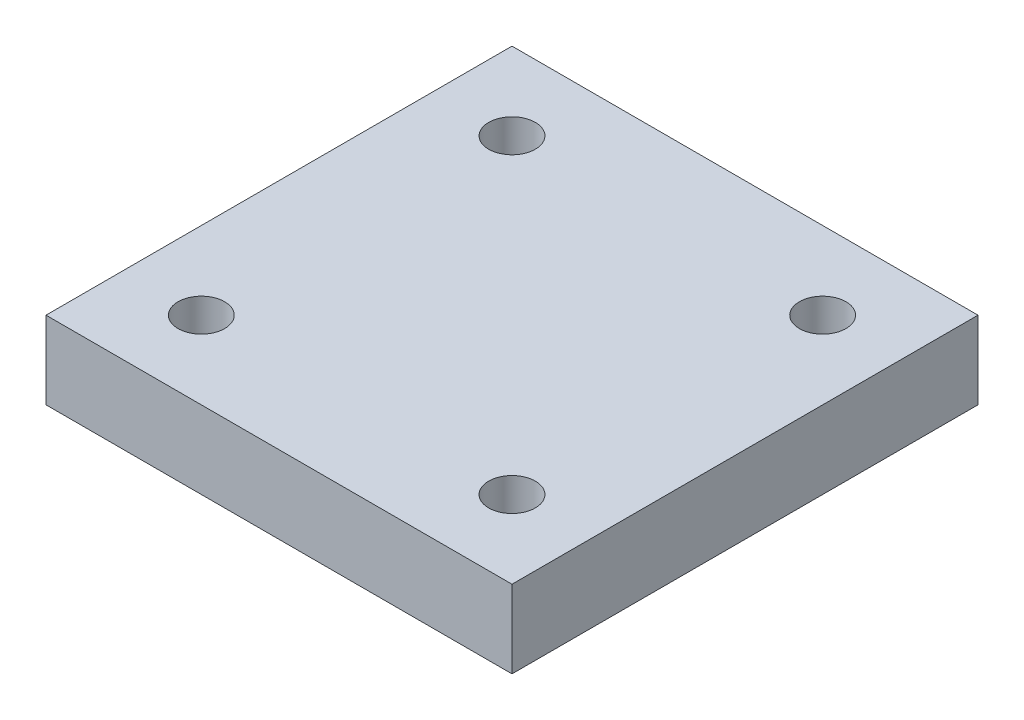
SolidWorks part; units mm, degrees
ref_plane "前视基准面" through (0, 0, 0) normal (0, 0, 1) x (1, 0, 0)
ref_plane "上视基准面" through (0, 0, 0) normal (0, 1, 0) x (1, 0, 0)
ref_plane "右视基准面" through (0, 0, 0) normal (1, 0, 0) x (0, 0, -1)
sketch "草图1" plane through (0, 0, 0) normal (0, 1, 0) x (1, 0, 0)
  line L0 (0, 15) -> (0, -15) construction
  line L1 (15, -15) -> (-15, -15)
  line L2 (15, -15) -> (15, 15)
  line L3 (15, 15) -> (-15, 15)
  line L4 (-15, -15) -> (-15, 15)
  line L5 (15, -15) -> (-15, 15) construction
  line L6 (15, 15) -> (-15, -15) construction
  line L7 (-15, 0) -> (15, 0) construction
  circle A0 centre (-10, 10) radius 1.5
  circle A1 centre (10, 10) radius 1.5
  circle A2 centre (10, -10) radius 1.5
  circle A3 centre (-10, -10) radius 1.5
  point P0 (0, 0)
  dimension "D3" = 3
  dimension "D1" = 30
  dimension "D2" = 30
  dimension "D4" = 10
  dimension "D5" = 10
extrude "凸台-拉伸1" add sketch "草图1" along normal blind 5
